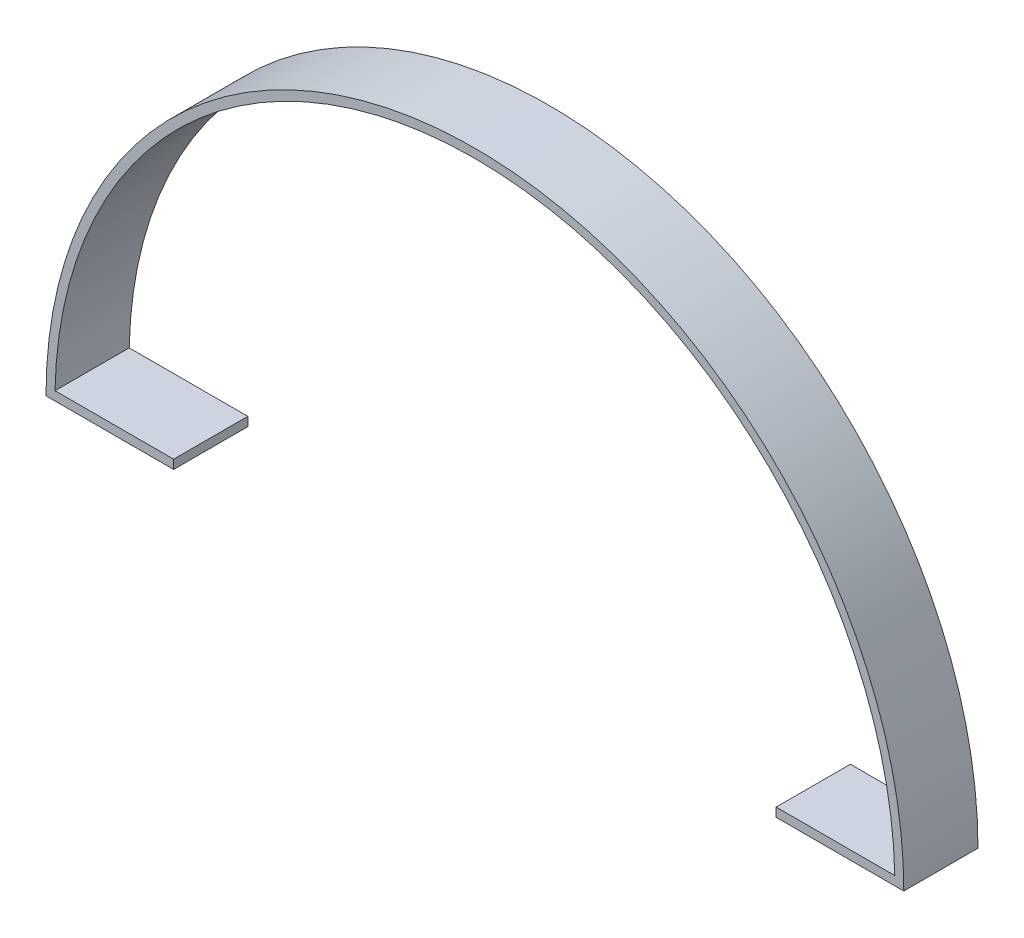
SolidWorks part; units mm, degrees
ref_plane "Plan de face" through (0, 0, 0) normal (0, 0, 1) x (1, 0, 0)
ref_plane "Plan de dessus" through (0, 0, 0) normal (0, 1, 0) x (1, 0, 0)
ref_plane "Plan de droite" through (0, 0, 0) normal (1, 0, 0) x (0, 0, -1)
sketch "Esquisse1" plane through (0, 0, 0) normal (0, 0, 1) x (1, 0, 0)
  line L0 (0, 0) -> (43, 0)
  line L1 (289, 0) -> (246, 0)
  arc A0 (0, 0) -> (289, 0) centre (144.5, 0) cw
  dimension "D1" = 289
  dimension "D2" = 43
extrude "Extru.-Mince1" add sketch "Esquisse1" along normal blind 25 thin thin type one direction wall 3
